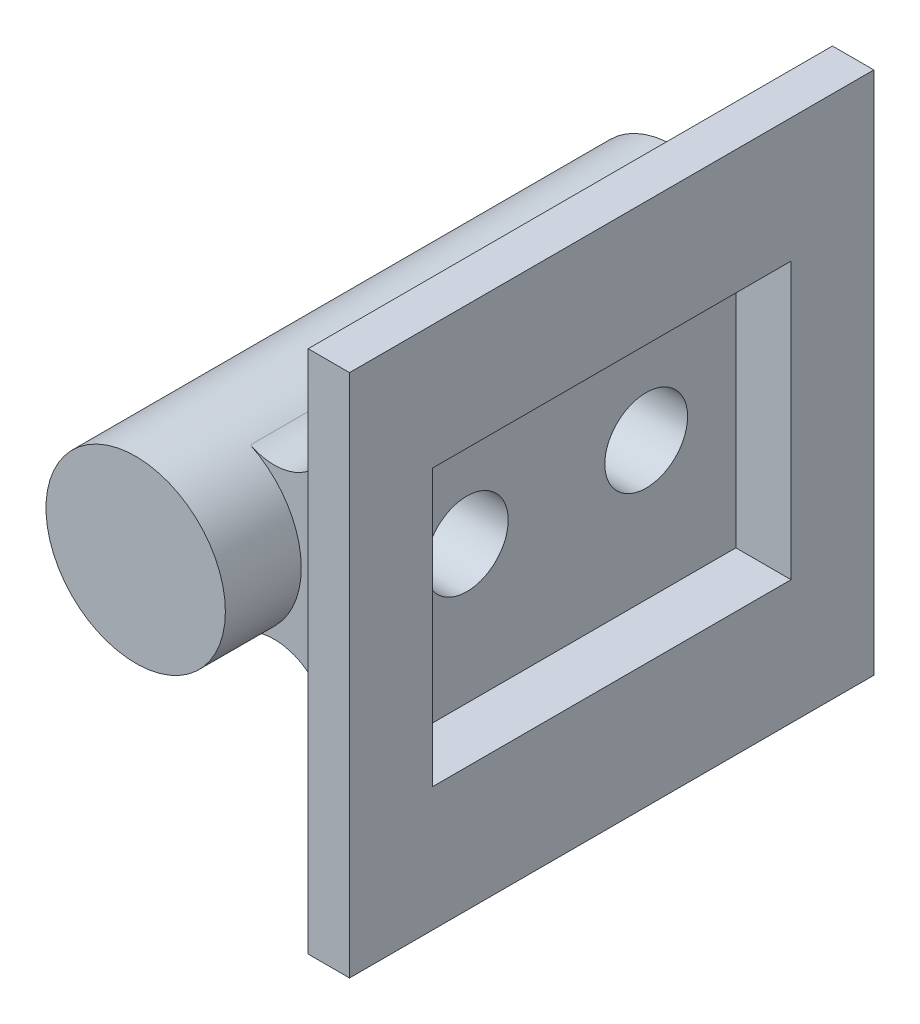
SolidWorks part; units mm, degrees
material "ABS"
ref_plane "正面" through (0, 0, 0) normal (0, 0, 1) x (1, 0, 0)
ref_plane "平面" through (0, 0, 0) normal (0, 1, 0) x (1, 0, 0)
ref_plane "右側面" through (0, 0, 0) normal (1, 0, 0) x (0, 0, -1)
sketch "ｽｹｯﾁ1" plane through (0, 0, 0) normal (0, 0, 1) x (1, 0, 0)
  circle A0 centre (0, 0) radius 3.25
  dimension "D1" = 6.5
extrude "ﾎﾞｽ - 押し出し1" add sketch "ｽｹｯﾁ1" along normal blind 19.5
ref_plane "平面1" through (5, 0, 0) normal (1, 0, 0) x (0, 0, -1)
sketch "ｽｹｯﾁ2" plane through (5, 0, 0) normal (1, 0, 0) x (0, 0, -1)
  line L0 (-19.5, 0) -> (0, 0) construction
  line L1 (-19.5, 3.25) -> (-19.5, -3.25) construction
  line L3 (-2.75, -6) -> (-16.75, -6)
  line L4 (-2.75, -6) -> (-2.75, 6)
  line L5 (-2.75, 6) -> (-16.75, 6)
  line L6 (-16.75, -6) -> (-16.75, 6)
  line L7 (-2.75, -6) -> (-16.75, 6) construction
  line L8 (-2.75, 6) -> (-16.75, -6) construction
  point P5 (-9.75, 0)
  dimension "D1" = 12
  dimension "D2" = 14
extrude "ﾎﾞｽ - 押し出し2" add sketch "ｽｹｯﾁ2" along normal blind 1 separate body
sketch "ｽｹｯﾁ3" plane through (0, 0, 2.75) normal (0, 0, -1) x (-1, 0, 0)
  line L0 (0, 0) -> (-5, 4.5)
  line L1 (-5, 3.575) -> (-5, -3.575) construction
  line L2 (-5, 4.5) -> (-5, -4.5)
  line L3 (-5, -4.5) -> (0, 0)
  dimension "D1" = 9
extrude "ﾎﾞｽ - 押し出し3" add sketch "ｽｹｯﾁ3" against normal up to surface (14 mm away) up to face at (5.5, 0, 16.75)
fillet "ﾌｨﾚｯﾄ1" radius 2 4 edges at (5, -4.5, 9.75) (2.4157, -2.1741, 9.75) (2.4157, 2.1741, 9.75) (5, 4.5, 9.75)
sketch "ｽｹｯﾁ5" plane through (6, 0, 0) normal (1, 0, 0) x (0, 0, -1)
  line L0 (-16.75, 0) -> (-2.75, 0) construction
  line L1 (-16.75, 6) -> (-16.75, -6) construction
  line L2 (-2.75, -2.9305) -> (-2.75, 2.9305) construction
  line L4 (-0.25, -9.5) -> (-19.25, -9.5)
  line L5 (-0.25, -9.5) -> (-0.25, 9.5)
  line L6 (-0.25, 9.5) -> (-19.25, 9.5)
  line L7 (-19.25, -9.5) -> (-19.25, 9.5)
  line L8 (-0.25, -9.5) -> (-19.25, 9.5) construction
  line L9 (-0.25, 9.5) -> (-19.25, -9.5) construction
  point P6 (-9.75, 0)
  dimension "D1" = 19
  dimension "D2" = 19
extrude "ﾎﾞｽ - 押し出し4" add sketch "ｽｹｯﾁ5" along normal blind 1.5
sketch "ｽｹｯﾁ6" plane through (7.5, 0, 0) normal (1, 0, 0) x (0, 0, -1)
  line L0 (-19.25, 0) -> (-0.25, 0) construction
  line L1 (-19.25, 9.5) -> (-19.25, -9.5) construction
  line L2 (-0.25, -9.5) -> (-0.25, 9.5) construction
  circle A0 centre (-13, 0) radius 1.5
  circle A1 centre (-6.5, 0) radius 1.5
  point P8 (-9.75, 0)
  dimension "D1" = 3
  dimension "D2" = 3.25
  dimension "D3" = 3.25
extrude "ｶｯﾄ - 押し出し1" cut sketch "ｽｹｯﾁ6" against normal through all
sketch "ｽｹｯﾁ7" plane through (7.5, 0, 0) normal (1, 0, 0) x (0, 0, -1)
  line L0 (-19.25, 0) -> (-0.25, 0) construction
  line L5 (-3.25, -5) -> (-16.25, -5)
  line L6 (-3.25, -5) -> (-3.25, 5)
  line L7 (-3.25, 5) -> (-16.25, 5)
  line L8 (-16.25, -5) -> (-16.25, 5)
  line L9 (-3.25, -5) -> (-16.25, 5) construction
  line L10 (-3.25, 5) -> (-16.25, -5) construction
  point P0 (-9.75, 0)
  dimension "D1" = 13
  dimension "D2" = 10
extrude "ｶｯﾄ - 押し出し2" cut sketch "ｽｹｯﾁ7" against normal blind 2
equation "\"D3@ｽｹｯﾁ6\"=\"D2@ｽｹｯﾁ6\""
